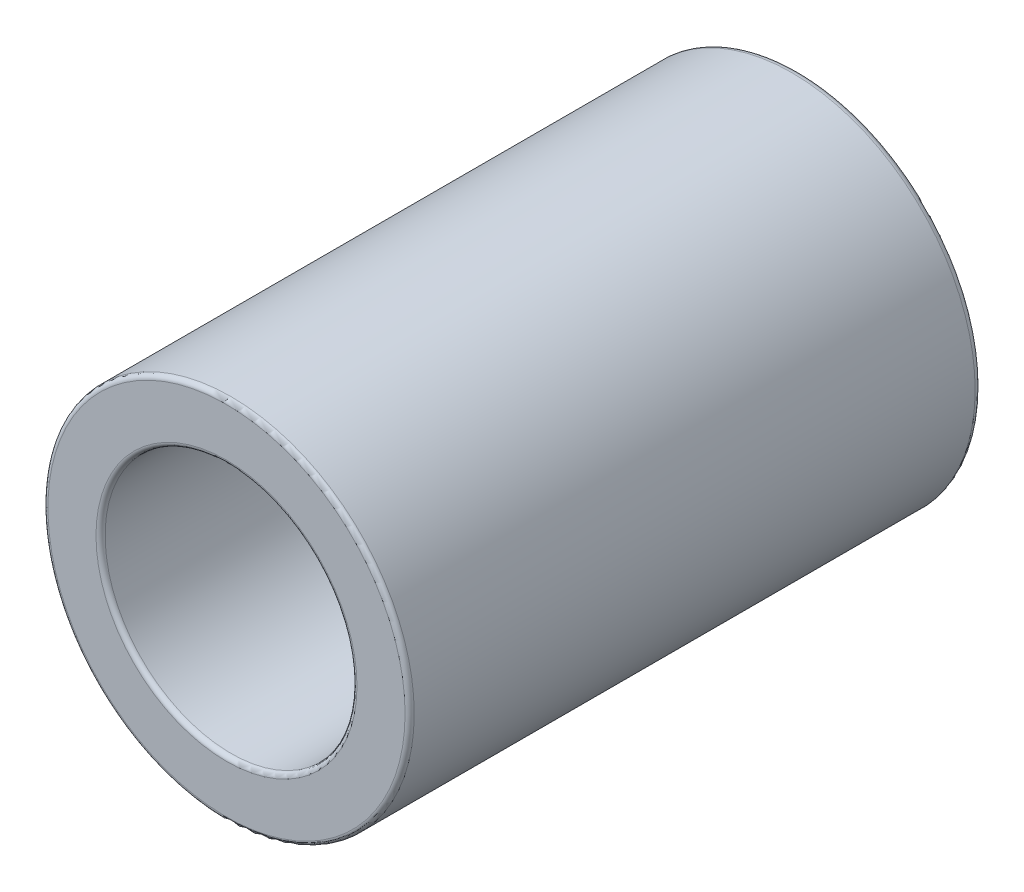
SolidWorks part; units mm, degrees
ref_plane "Front Plane" through (0, 0, 0) normal (0, 0, 1) x (1, 0, 0)
ref_plane "Top Plane" through (0, 0, 0) normal (0, 1, 0) x (1, 0, 0)
ref_plane "Right Plane" through (0, 0, 0) normal (1, 0, 0) x (0, 0, -1)
sketch "Sketch1" plane through (0, 0, 0) normal (0, 0, 1) x (1, 0, 0)
  circle A0 centre (0, 0) radius 8
  dimension "D1" = 16
extrude "Boss-Extrude1" add sketch "Sketch1" along normal blind 25
sketch "Sketch2" plane through (0, 0, 25) normal (0, 0, 1) x (1, 0, 0)
  circle A0 centre (0, 0) radius 5.5
  dimension "D1" = 11
extrude "Cut-Extrude1" cut sketch "Sketch2" against normal blind 20
sketch "Sketch3" plane through (0, 0, 5) normal (0, 0, 1) x (1, 0, 0)
  circle A0 centre (0, 0) radius 2.5
  dimension "D1" = 5
extrude "Cut-Extrude2" cut sketch "Sketch3" against normal through all
fillet "Fillet1" radius 0.2 4 edges at (8, 0, 25) (5.5, 0, 25) (2.5, 0, 0) (2.5, 0, 5)
fillet "Fillet2" radius 0.3 1 edges at (8, 0, 0)
sketch "Sketch4" plane through (0, 0, 0) normal (0, 1, 0) x (1, 0, 0)
  line L0 (0, -28.9233) -> (0, 2.5354) construction
